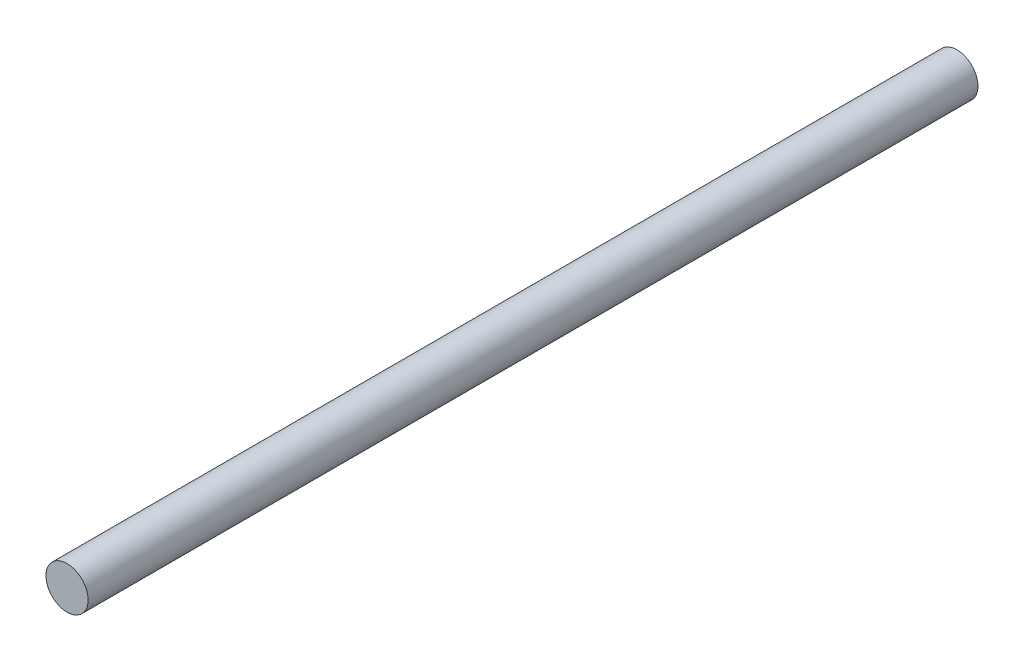
SolidWorks part; units mm, degrees
ref_plane "Front Plane" through (0, 0, 0) normal (0, 0, 1) x (1, 0, 0)
ref_plane "Top Plane" through (0, 0, 0) normal (0, 1, 0) x (1, 0, 0)
ref_plane "Right Plane" through (0, 0, 0) normal (1, 0, 0) x (0, 0, -1)
sketch "Sketch1" plane through (0, 0, 0) normal (0, 0, 1) x (1, 0, 0)
  circle A0 centre (0, 0) radius 2.286
  dimension "D1" = 4.572
extrude "Boss-Extrude1" add sketch "Sketch1" along normal blind 96.52
